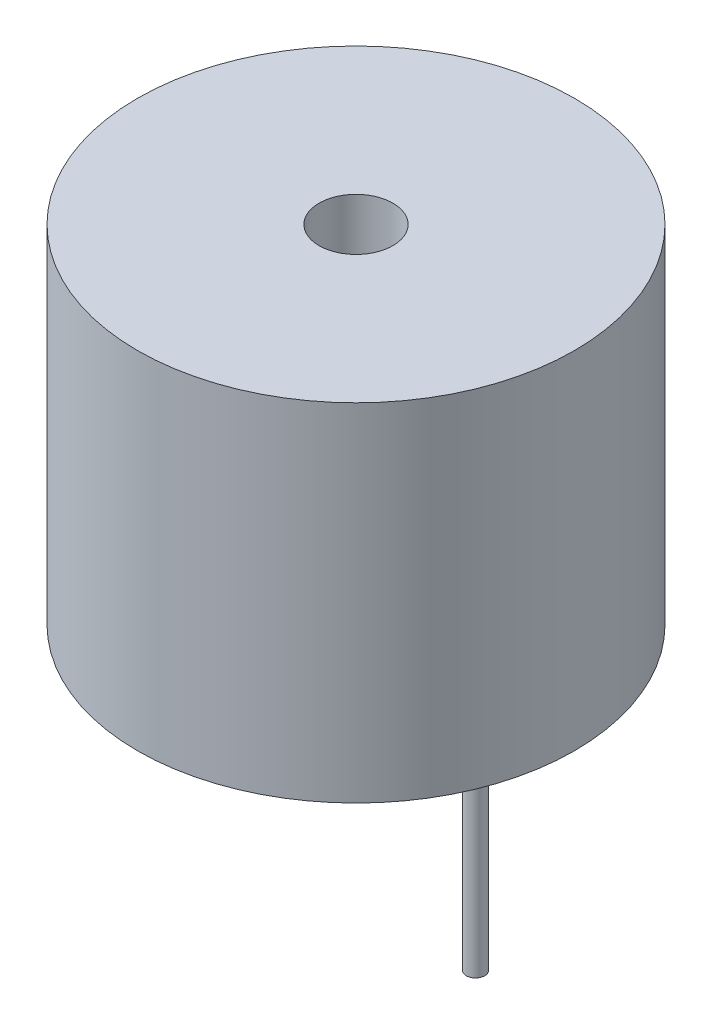
SolidWorks part; units mm, degrees
ref_plane "Alzado" through (0, 0, 0) normal (0, 0, 1) x (1, 0, 0)
ref_plane "Planta" through (0, 0, 0) normal (0, 1, 0) x (1, 0, 0)
ref_plane "Vista lateral" through (0, 0, 0) normal (1, 0, 0) x (0, 0, -1)
sketch "Croquis1" plane through (0, 0, 0) normal (0, 1, 0) x (1, 0, 0)
  circle A0 centre (0, 0) radius 5.925
  dimension "D1" = 11.85
extrude "Saliente-Extruir1" add sketch "Croquis1" along normal blind 9.4 contours A0
sketch "Croquis2" plane through (0, 0, 0) normal (0, -1, 0) x (1, 0, 0)
  circle A0 centre (-3.2418, 0) radius 0.25
  dimension "D1" = 0.5
extrude "Saliente-Extruir2" add sketch "Croquis2" along normal blind 4.9 contours A0
sketch "Croquis3" plane through (0, 0, 0) normal (0, -1, 0) x (1, 0, 0)
  circle A0 centre (3.2418, 0) radius 0.25
extrude "Saliente-Extruir3" add sketch "Croquis3" along normal blind 6.5
sketch "Croquis4" plane through (0, 9.4, 0) normal (0, 1, 0) x (1, 0, 0)
  circle A0 centre (0, 0) radius 1
  dimension "D1" = 2
extrude "Cortar-Extruir1" cut sketch "Croquis4" against normal blind 4.5
sketch "Sketch1" plane through (0, 9.4, 0) normal (0, 1, 0) x (1, 0, 0)
  point P0 (0, 0)
